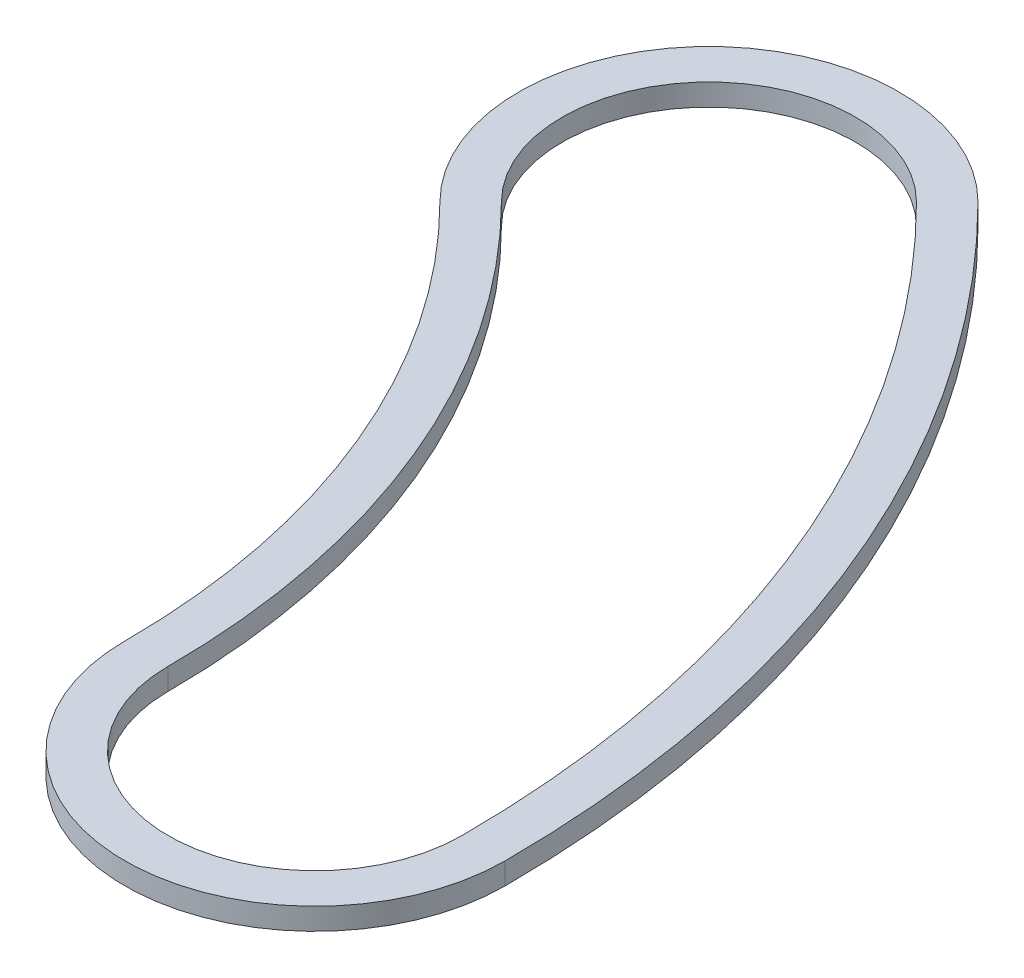
SolidWorks part; units mm, degrees
material "NBR"
ref_plane "Front Plane" through (0, 0, 0) normal (0, 0, 1) x (1, 0, 0)
ref_plane "Top Plane" through (0, 0, 0) normal (0, 1, 0) x (1, 0, 0)
ref_plane "Right Plane" through (0, 0, 0) normal (1, 0, 0) x (0, 0, -1)
sketch "Sketch1" plane through (0, 0, 0) normal (0, 1, 0) x (1, 0, 0)
  line L0 (0, 0) -> (15.7154, 15.7154) construction
  line L1 (0, 0) -> (22.225, 0) construction
  arc A0 (22.225, 0) -> (15.7154, 15.7154) centre (0, 0) ccw construction
  arc A1 (26.67, 0) -> (18.8585, 18.8585) centre (0, 0) ccw
  arc A2 (17.78, 0) -> (12.5724, 12.5724) centre (0, 0) ccw
  arc A3 (17.78, 0) -> (26.67, 0) centre (22.225, 0) ccw
  arc A4 (18.8585, 18.8585) -> (12.5724, 12.5724) centre (15.7154, 15.7154) ccw
  arc A5 (22.225, 0) -> (15.7154, 15.7154) centre (0, 0) ccw construction
  arc A6 (25.654, 0) -> (18.1401, 18.1401) centre (0, 0) ccw
  arc A7 (18.796, 0) -> (13.2908, 13.2908) centre (0, 0) ccw
  arc A8 (18.796, 0) -> (25.654, 0) centre (22.225, 0) ccw
  arc A9 (18.1401, 18.1401) -> (13.2908, 13.2908) centre (15.7154, 15.7154) ccw
  point P4 (20.5332, 8.5051)
  point P13 (20.5332, 8.5051)
  dimension "D4" = 22.225
  dimension "D3" = 4.445
  dimension "D1" = 45
  dimension "D2" = 1.016
extrude "Boss-Extrude1" add sketch "Sketch1" along normal blind 0.508
equation "\"w\"= 0.04"
equation "\"D2@Sketch1\"=\"w\""
equation "\"D3@Sketch1\"= .185 - .01 '10 thou smaller than channel rad"
